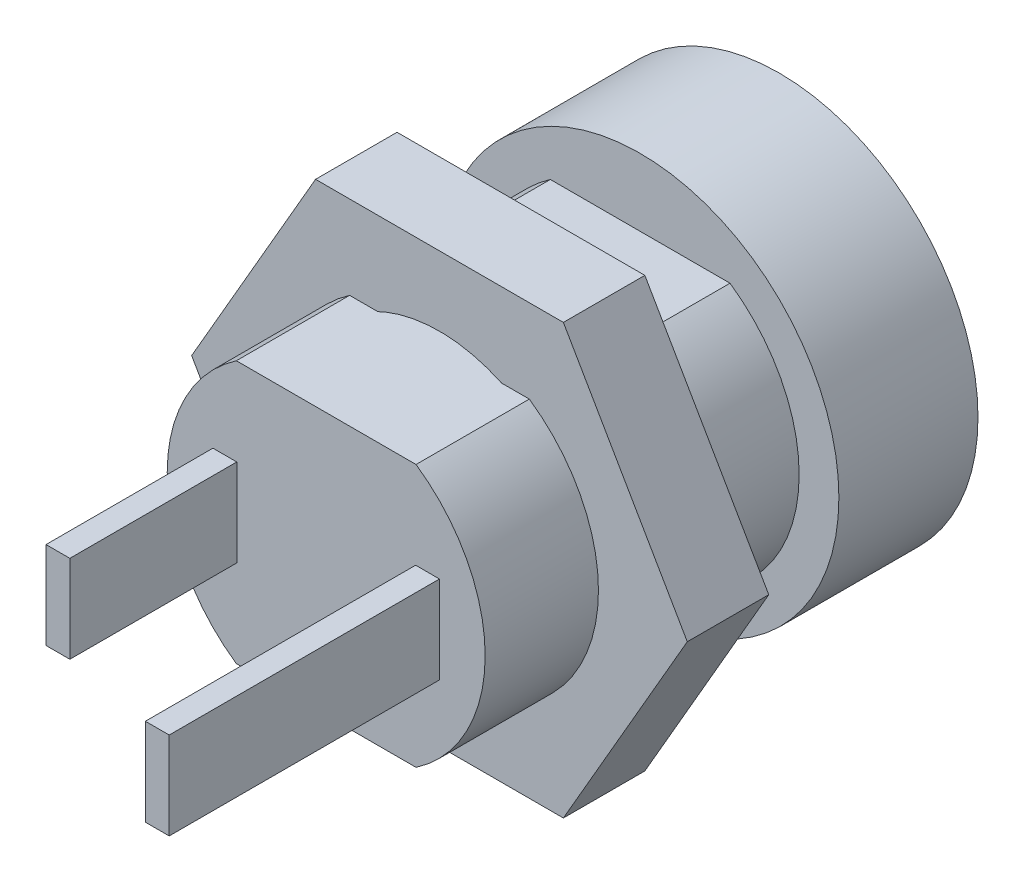
SolidWorks part; units mm, degrees
material "Лист Д16А.Т хх ГОСТ 21631-76"
ref_plane "Front" through (0, 0, 0) normal (0, 0, 1) x (1, 0, 0)
ref_plane "Top" through (0, 0, 0) normal (0, 1, 0) x (1, 0, 0)
ref_plane "Right" through (0, 0, 0) normal (1, 0, 0) x (0, 0, -1)
sketch "Эскиз3" plane through (0, 0, 0) normal (1, 0, 0) x (0, 0, -1)
  line L0 (0, 0) -> (11.9, 0) construction
  line L1 (11.9, 0) -> (11.9, 5)
  line L2 (11.9, 5) -> (7.9, 5)
  line L3 (7.9, 5) -> (7.9, 4)
  line L4 (7.9, 4) -> (0, 4)
  line L5 (0, 4) -> (0, 0)
  line L6 (0, 0) -> (11.9, 0)
  dimension "D1" = 11.9
  dimension "D2" = 10
  dimension "D3" = 4
  dimension "D4" = 8
revolve "Повернуть1" add sketch "Эскиз3" angle 360 about L0
sketch "Эскиз4" plane through (0, 0, 0) normal (0, 0, 1) x (1, 0, 0)
  line L0 (0, 0) -> (0, 1.9294) construction
  line L1 (-2.25, -1.1) -> (-2.85, -1.1)
  line L2 (-2.25, -1.1) -> (-2.25, 1.1)
  line L3 (-2.25, 1.1) -> (-2.85, 1.1)
  line L4 (-2.85, -1.1) -> (-2.85, 1.1)
  line L5 (-2.55, 1.1) -> (-2.55, -1.1) construction
  line L6 (-2.25, 0) -> (-2.85, 0) construction
  line L7 (2.85, -1.1) -> (2.25, -1.1)
  line L8 (2.85, -1.1) -> (2.85, 1.1)
  line L9 (2.85, 1.1) -> (2.25, 1.1)
  line L10 (2.25, -1.1) -> (2.25, 1.1)
  line L11 (2.55, 1.1) -> (2.55, -1.1) construction
  line L12 (2.85, 0) -> (2.25, 0) construction
  point P0 (-2.55, 0)
  point P4 (2.55, 0)
  dimension "D1" = 0.6
  dimension "D2" = 2.2
  dimension "D3" = 5.7
extrude "Бобышка-Вытянуть2" add sketch "Эскиз4" along normal blind 4.2
sketch "Эскиз5" plane through (0, 0, 4.2) normal (0, 0, 1) x (1, 0, 0)
  line L4 (2.25, 1.1) -> (2.25, -1.1)
  line L5 (2.25, -1.1) -> (2.85, -1.1)
  line L6 (2.85, -1.1) -> (2.85, 1.1)
  line L7 (2.85, 1.1) -> (2.25, 1.1)
  line L8 (2.25, 1.1) -> (2.25, -1.1)
  line L9 (2.25, -1.1) -> (2.85, -1.1)
  line L10 (2.85, -1.1) -> (2.85, 1.1)
  line L11 (2.85, 1.1) -> (2.25, 1.1)
  dimension "D1" = 0
extrude "Бобышка-Вытянуть3" add sketch "Эскиз5" along normal blind 2.6
sketch "Эскиз7" plane through (0, 0, -11.9) normal (0, 0, -1) x (-1, 0, 0)
  circle A0 centre (0, 0) radius 2.75
  circle A1 centre (0, 0) radius 1
  dimension "D1" = 5.5
  dimension "D2" = 2
extrude "Вырез-Вытянуть2" cut sketch "Эскиз7" against normal blind 5
sketch "Эскиз8" plane through (0, 0, -11.9) normal (0, 0, -1) x (-1, 0, 0)
  circle A0 centre (0, 0) radius 4.45
  circle A1 centre (0, 0) radius 5
  circle A2 centre (0, 0) radius 5
  dimension "D2" = 8.9
  dimension "D1" = 0
extrude "Вырез-Вытянуть3" cut sketch "Эскиз8" against normal blind 0.5
chamfer "Фаска1" distance 0.4 angle 45 1 edges at (-4.45, 0, -11.9)
sketch "Эскиз9" plane through (0, 0, 0) normal (0, 0, 1) x (1, 0, 0)
  line L1 (4, -3.3) -> (-4, -3.3)
  line L2 (4, -3.3) -> (4, 3.3)
  line L3 (4, 3.3) -> (-4, 3.3)
  line L4 (-4, -3.3) -> (-4, 3.3)
  line L5 (0, 3.3) -> (0, -3.3) construction
  line L6 (4, 0) -> (-4, 0) construction
  circle A0 centre (0, 0) radius 4 construction
  circle A1 centre (0, 0) radius 4 construction
  point P0 (0, 0)
  point P4 (-4, 0)
  dimension "D1" = 6.6
extrude "Вырез-Вытянуть4" cut sketch "Эскиз9" against normal up to surface (7.9 mm away) flip side to cut up to face at (4, 0, -7.9)
sketch "Эскиз10" plane through (0, 0, -7.9) normal (0, 0, 1) x (1, 0, 0)
  line L1 (-6.2354, 0) -> (-3.1177, -5.4)
  line L2 (-3.1177, -5.4) -> (3.1177, -5.4)
  line L3 (3.1177, -5.4) -> (6.2354, 0)
  line L4 (6.2354, 0) -> (3.1177, 5.4)
  line L5 (3.1177, 5.4) -> (-3.1177, 5.4)
  line L6 (-3.1177, 5.4) -> (-6.2354, 0)
  circle A0 centre (0, 0) radius 5.4 construction
  circle A1 centre (0, 0) radius 3.65
  dimension "D1" = 7.3
  dimension "D2" = 10.8
extrude "Бобышка-Вытянуть4" add sketch "Эскиз10" along normal blind 2.05 from offset 3 separate body
